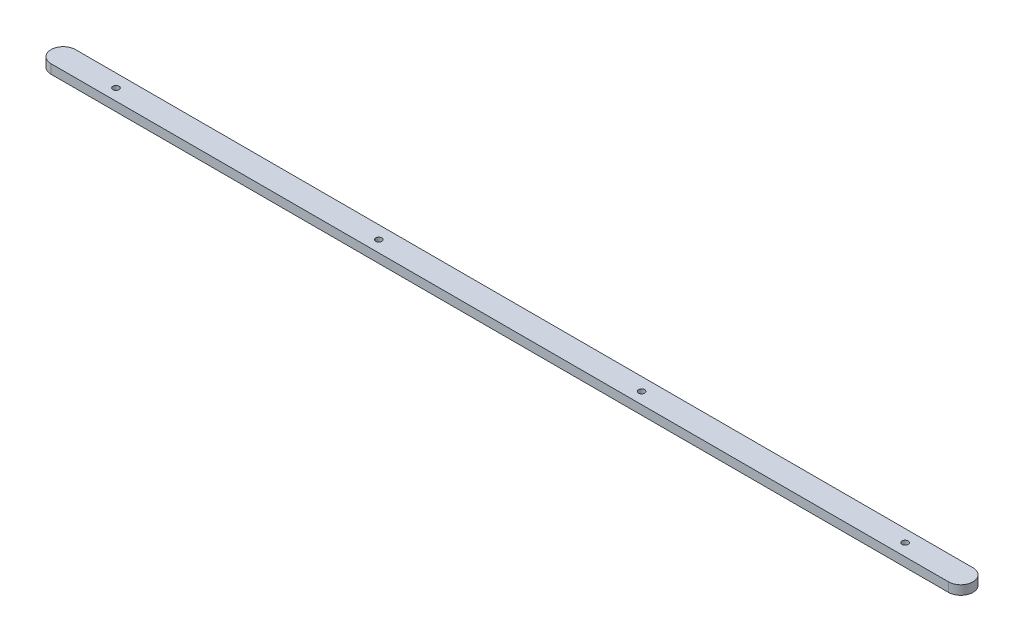
SolidWorks part; units mm, degrees
ref_plane "Front Plane" through (0, 0, 0) normal (0, 0, 1) x (1, 0, 0)
ref_plane "Top Plane" through (0, 0, 0) normal (0, 1, 0) x (1, 0, 0)
ref_plane "Right Plane" through (0, 0, 0) normal (1, 0, 0) x (0, 0, -1)
sketch "Sketch1" plane through (0, 0, 0) normal (0, 1, 0) x (1, 0, 0)
  line L0 (-146.3456, -7.3602) -> (147.3537, -7.3602)
  line L1 (147.3537, 0.6398) -> (-146.3456, 0.6398)
  arc A0 (-146.3456, 0.6398) -> (-150.3456, -3.3602) centre (-146.3456, -3.3602) ccw
  arc A1 (-150.3456, -3.3602) -> (-146.3456, -7.3602) centre (-146.3456, -3.3602) ccw
  arc A2 (147.3537, -7.3602) -> (151.3537, -3.3602) centre (147.3537, -3.3602) ccw
  arc A3 (151.3537, -3.3602) -> (147.3537, 0.6398) centre (147.3537, -3.3602) ccw
  circle A4 centre (-128.8456, -3.6102) radius 1
  circle A5 centre (-42.8456, -3.6102) radius 1
  circle A6 centre (43.1544, -3.6102) radius 1
  circle A7 centre (129.1544, -3.3602) radius 1
extrude "Boss-Extrude1" add sketch "Sketch1" along normal blind 3
